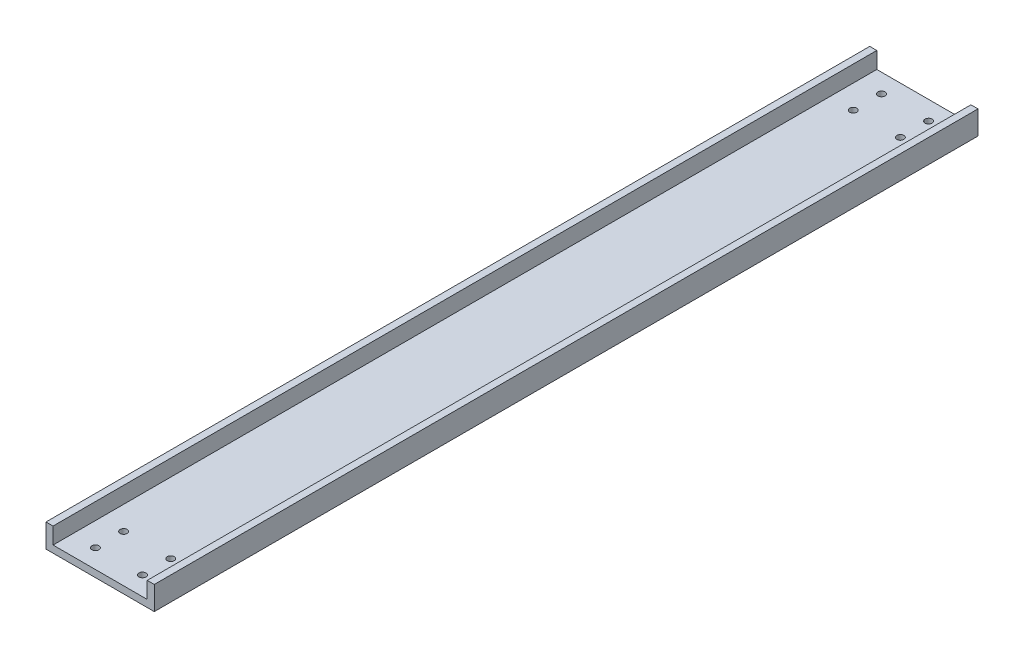
SolidWorks part; units mm, degrees
ref_plane "Front Plane" through (0, 0, 0) normal (0, 0, 1) x (1, 0, 0)
ref_plane "Top Plane" through (0, 0, 0) normal (0, 1, 0) x (1, 0, 0)
ref_plane "Right Plane" through (0, 0, 0) normal (1, 0, 0) x (0, 0, -1)
sketch "Sketch2" plane through (0, 0, 0) normal (0, 0, 1) x (1, 0, 0)
  line L0 (0, 0) -> (0, 7)
  line L1 (0, 7) -> (-3, 7)
  line L2 (-3, 7) -> (-3, -3)
  line L3 (-3, -3) -> (43, -3)
  line L4 (43, -3) -> (43, 7)
  line L5 (43, 7) -> (40, 7)
  line L6 (40, 7) -> (40, 0)
  line L7 (40, 0) -> (0, 0)
  dimension "D1" = 3
  dimension "D2" = 3
  dimension "D3" = 3
  dimension "D4" = 10
  dimension "D5" = 40
extrude "Boss-Extrude1" add sketch "Sketch2" along normal blind 350
hole_wizard "Ø3.0mm Dowel Hole1" positions "Sketch4" profile "Sketch3" hole size "Ø3.0" standard "ISO"
sketch "Sketch4" plane through (0, -3, 0) normal (0, -1, 0) x (-1, 0, 0)
  line L1 (-43, -350) -> (-43, 0) construction
  line L2 (3, -350) -> (-43, -350) construction
  point P0 (-10, -342)
  point P2 (-30, -342)
  point P4 (-30, -330)
  point P6 (-10, -330)
  dimension "D1" = 20
  dimension "D2" = 13
  dimension "D3" = 8
  dimension "D4" = 12
sketch "Sketch3" plane through (10, -3, 342) normal (1, 0, 0) x (0, 0, -1)
  line L0 (0, 0) -> (0, 15.9013)
  line L1 (0, 15.9013) -> (1.5, 15)
  line L2 (1.5, 15) -> (1.5, 0)
  line L5 (1.5, 0) -> (0, 0)
  line L10 (0, 15.9013) -> (-1.5, 15) construction
  line L11 (0, -6.35) -> (0, 107.95) construction
  dimension "Hole Dia." = 3
  dimension "Hole Depth" = 15
  dimension "Drill Angle" = 118
sketch "Sketch5" plane through (43, 0, 0) normal (1, 0, 0) x (0, 0, -1)
  line L0 (-175, 7) -> (-175, -3) construction
  line L1 (-350, 7) -> (0, 7) construction
  line L2 (-350, -3) -> (0, -3) construction
sketch "Sketch7" plane through (0, -3, 0) normal (0, -1, 0) x (1, 0, 0)
  line L0 (-3, 175) -> (43, 175) construction
  line L1 (-3, 350) -> (-3, 0) construction
  line L2 (43, 350) -> (43, 0) construction
ref_plane "Plane1" through (0, 0, 175) normal (0, 0, 1) x (1, 0, 0)
mirror "Mirror1" about plane through (0, 0, 175) normal (0, 0, 1) of "Ø3.0mm Dowel Hole1"
